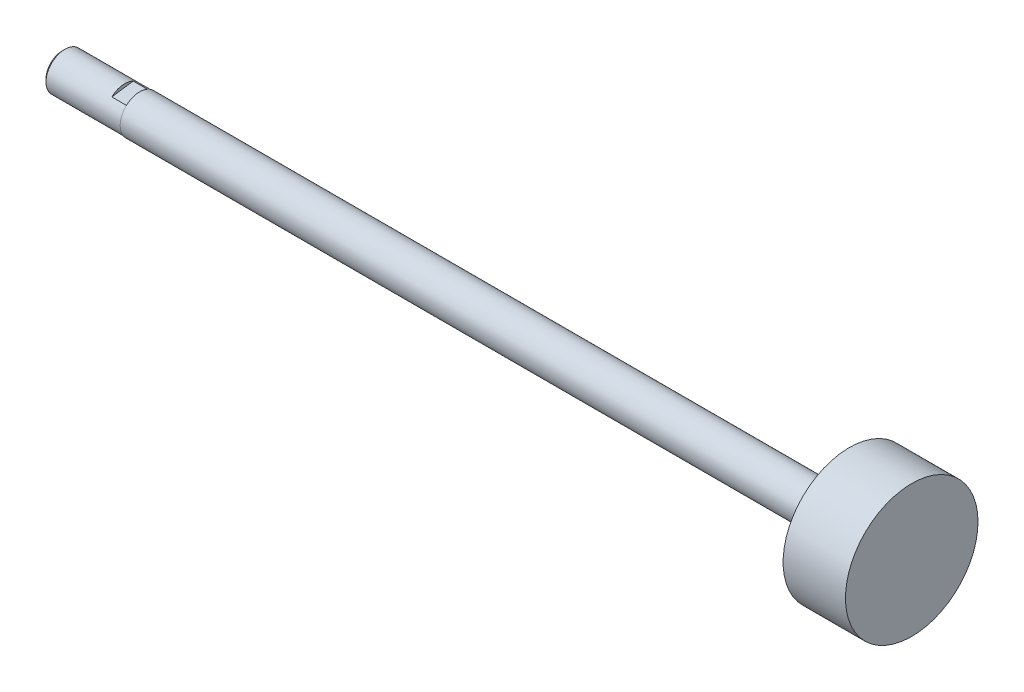
SolidWorks part; units mm, degrees
ref_plane "Front Plane" through (0, 0, 0) normal (0, 0, 1) x (1, 0, 0)
ref_plane "Top Plane" through (0, 0, 0) normal (0, 1, 0) x (1, 0, 0)
ref_plane "Right Plane" through (0, 0, 0) normal (1, 0, 0) x (0, 0, -1)
sketch "Sketch1" plane through (0, 0, 0) normal (0, 0, 1) x (1, 0, 0)
  line L0 (732.8499, 3.8633) -> (732.8499, 0)
  line L1 (732.8499, 0) -> (745.5499, 0)
  line L2 (745.5499, 0) -> (745.5499, 3.8633)
  line L3 (745.5499, 3.8633) -> (732.8499, 3.8633)
  line L4 (732.8499, 0) -> (745.5499, 0) construction
revolve "Revolve1" add sketch "Sketch1" angle 360 about L4
sketch "Sketch2" plane through (745.5499, 0, 0) normal (1, 0, 0) x (0, 0, -1)
  line L0 (2.6235, -2.8359) -> (-1.7354, -3.4516)
  line L1 (-2.6235, 2.8359) -> (1.7354, 3.4516)
  arc A0 (1.7354, 3.4516) -> (2.6235, -2.8359) centre (0, 0) cw
  arc A1 (-1.7354, -3.4516) -> (-2.6235, 2.8359) centre (0, 0) cw
extrude "Boss-Extrude1" add sketch "Sketch2" along normal blind 3.048
ref_plane "Plane1" through (748.5979, 0, 0) normal (-1, 0, 0) x (0, -1, 0)
sketch "Sketch3" plane through (748.5979, 0, 0) normal (-1, 0, 0) x (0, -1, 0)
  circle A0 centre (0, 0) radius 3.9624
extrude "Boss-Extrude2" add sketch "Sketch3" against normal blind 144.526
ref_plane "Plane2" through (893.1239, 0, 0) normal (-1, 0, 0) x (0, -1, 0)
sketch "Sketch4" plane through (893.1239, 0, 0) normal (-1, 0, 0) x (0, -1, 0)
  circle A0 centre (0, 0) radius 13.4938
extrude "Boss-Extrude3" add sketch "Sketch4" against normal blind 12.7
chamfer "Chamfer1" distance 0.5359 angle 45 1 edges at (732.8499, 3.8633, 0)
